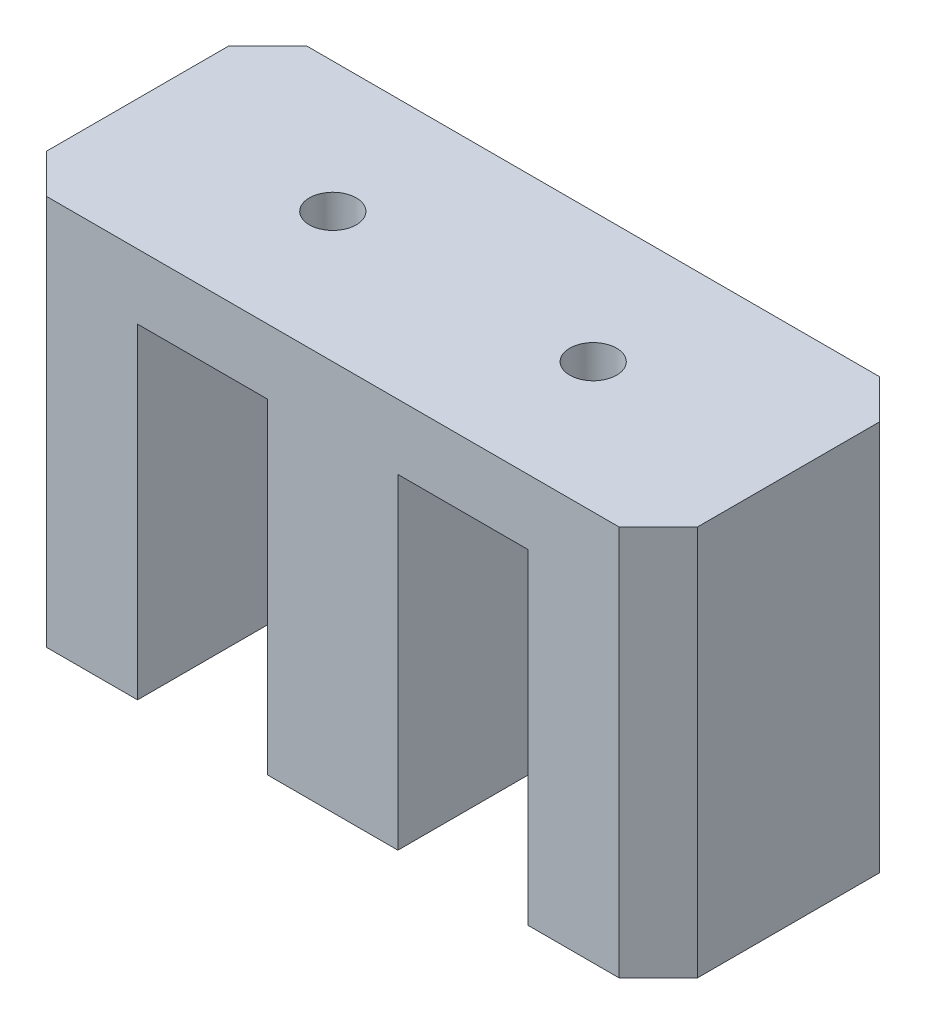
SolidWorks part; units mm, degrees
ref_plane "Ebene vorne" through (0, 0, 0) normal (0, 0, 1) x (1, 0, 0)
ref_plane "Ebene oben" through (0, 0, 0) normal (0, 1, 0) x (1, 0, 0)
ref_plane "Ebene rechts" through (0, 0, 0) normal (1, 0, 0) x (0, 0, -1)
sketch "Skizze1" plane through (0, 0, 0) normal (0, 1, 0) x (1, 0, 0)
  line L1 (-25, 10) -> (25, 10)
  line L2 (-25, 10) -> (-25, -10)
  line L3 (-25, -10) -> (25, -10)
  line L4 (25, 10) -> (25, -10)
  point P4 (0, 10)
  point P6 (25, 0)
  dimension "D1" = 50
  dimension "D2" = 20
extrude "Aufsatz-Linear austragen1" add sketch "Skizze1" along normal blind 30
sketch "Skizze2" plane through (0, 0, 0) normal (0, -1, 0) x (1, 0, 0)
  line L0 (-25, 10) -> (25, 10) construction
  line L1 (25, -10) -> (-25, -10) construction
  line L2 (-15, 10) -> (-5, 10)
  line L3 (-15, 10) -> (-15, -10)
  line L4 (-15, -10) -> (-5, -10)
  line L5 (-5, 10) -> (-5, -10)
  line L6 (-25, -10) -> (-25, 10) construction
  line L7 (5, 10) -> (15, 10)
  line L8 (5, 10) -> (5, -10)
  line L9 (5, -10) -> (15, -10)
  line L10 (15, 10) -> (15, -10)
  dimension "D1" = 10
  dimension "D2" = 10
  dimension "D4" = 10
  dimension "D5" = 10
extrude "Schnitt-Linear austragen1" cut sketch "Skizze2" against normal blind 25
hole_wizard "Durchgangsloch für M31" positions "Skizze3" profile "Skizze4" hole size "M3" standard "DIN" end condition through all
sketch "Skizze3" plane through (0, 30, 0) normal (0, 1, 0) x (1, 0, 0)
  point P0 (-10, 0)
  point P2 (10, 0)
  dimension "D1" = 20
  dimension "D2" = 10
sketch "Skizze4" plane through (-10, 30, 0) normal (1, 0, 0) x (0, 0, 1)
  line L0 (0, 0) -> (0, 30)
  line L1 (0, 30) -> (1.8, 30)
  line L2 (1.8, 30) -> (1.8, 0)
  line L5 (1.8, 0) -> (0, 0)
  line L11 (0, -6.35) -> (0, 107.95) construction
  dimension "Bohrerdurchmesser" = 3.6
  dimension "Bohrungstiefe" = 30
chamfer "Fase1" distance 3 angle 45 4 edges at (-25, 15, -10) (25, 15, -10) (25, 15, 10) (-25, 15, 10)
